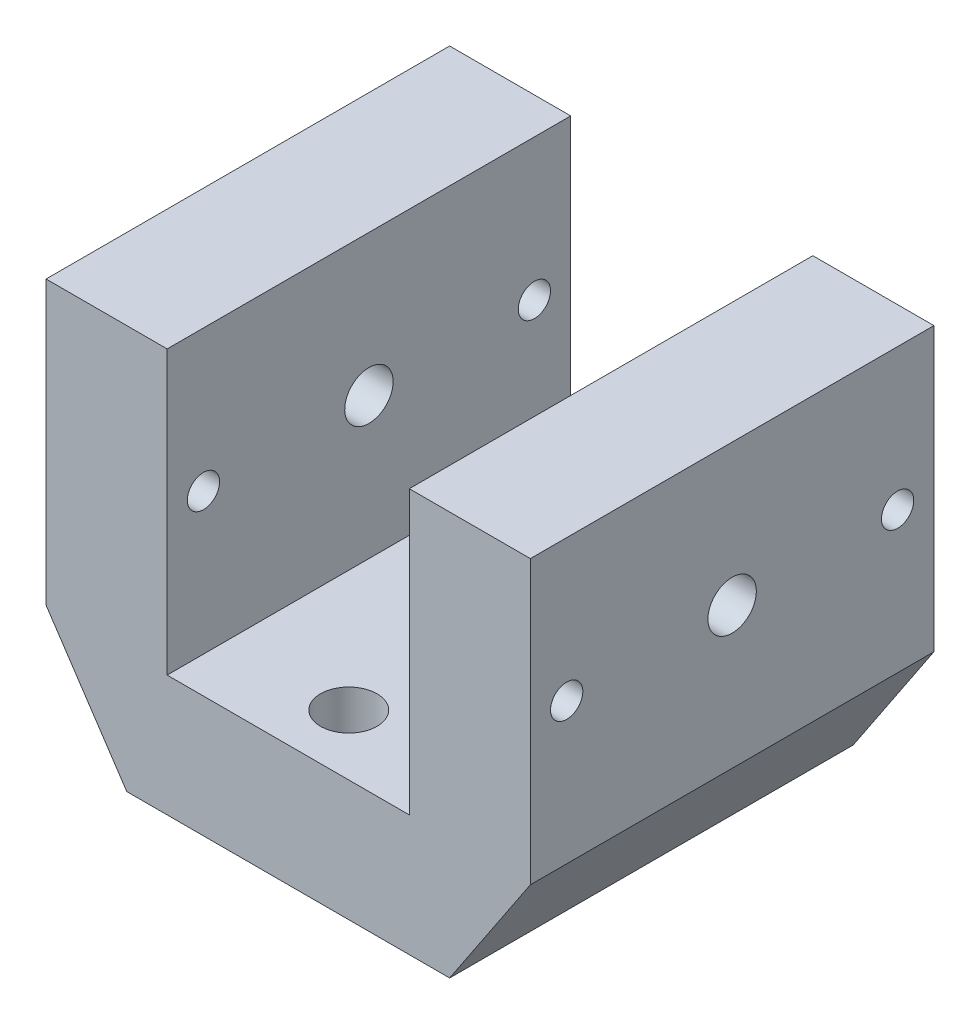
SolidWorks part; units mm, degrees
ref_plane "Płaszczyzna przednia" through (0, 0, 0) normal (0, 0, 1) x (1, 0, 0)
ref_plane "Płaszczyzna górna" through (0, 0, 0) normal (0, 1, 0) x (1, 0, 0)
ref_plane "Płaszczyzna prawa" through (0, 0, 0) normal (1, 0, 0) x (0, 0, -1)
sketch "Sketch1" plane through (0, 0, 0) normal (0, 0, 1) x (1, 0, 0)
  line L0 (-60, -50) -> (-60, 50)
  line L5 (-60, -50) -> (60, -50)
  line L7 (-60, 50) -> (60, 50)
  line L8 (60, -50) -> (60, 50)
  line L9 (-60, -50) -> (60, 50) construction
  line L10 (-60, 50) -> (60, -50) construction
  point P1 (0, 0)
  dimension "D1" = 100
  dimension "D2" = 120
extrude "Boss-Extrude1" add sketch "Sketch1" along normal blind 100
sketch "Sketch2" plane through (0, 0, 0) normal (0, 0, 1) x (1, 0, 0)
  line L24 (0, 50) -> (0, -50) construction
  line L25 (-60, -50) -> (60, -50) construction
  line L26 (-60, -20) -> (-40, -50)
  line L27 (-60, 50) -> (-60, -50) construction
  line L28 (30, 50) -> (30, -20)
  line L29 (-60, -20) -> (-60, -50)
  line L30 (-60, -50) -> (-40, -50)
  line L31 (-30, 50) -> (-30, -20)
  line L32 (60, 50) -> (-60, 50) construction
  line L33 (-30, -20) -> (30, -20)
  line L34 (-30, 50) -> (30, 50)
  line L35 (60, -50) -> (40, -50)
  line L36 (60, -20) -> (60, -50)
  line L37 (60, -20) -> (40, -50)
  point P18 (0, 0)
  dimension "D1" = 20
  dimension "D2" = 30
  dimension "D3" = 30
extrude "Cut-Extrude2" cut sketch "Sketch2" along normal through all both and the other way through all
sketch "Sketch3" plane through (0, 0, 0) normal (0, 1, 0) x (1, 0, 0)
  line L0 (-60, -50) -> (60, -50) construction
  line L1 (-60, -100) -> (-60, 0) construction
  line L2 (60, -100) -> (60, 0) construction
  line L3 (0, 0) -> (0, -100) construction
  line L4 (30, 0) -> (-30, 0) construction
  line L5 (-30, -100) -> (30, -100) construction
  circle A1 centre (0, -85) radius 4
  circle A2 centre (0, -15) radius 4
  dimension "D1" = 35
  dimension "D3" = 8
  dimension "D2" = 35
extrude "Cut-Extrude3" cut sketch "Sketch3" against normal through all both
sketch "Sketch5" plane through (0, 0, 0) normal (1, 0, 0) x (0, 0, -1)
  line L0 (-100, 15) -> (0, 15) construction
  line L1 (-100, -20) -> (-100, 50) construction
  line L2 (0, -20) -> (0, 50) construction
  circle A0 centre (-91, 15) radius 4
  circle A1 centre (-9, 15) radius 4
  dimension "D1" = 8
  dimension "D2" = 9
  dimension "D3" = 9
extrude "Cut-Extrude4" cut sketch "Sketch5" against normal through all both and the other way through all
sketch "Sketch6" plane through (0, 0, 0) normal (1, 0, 0) x (0, 0, -1)
  line L0 (-100, 15) -> (0, 15) construction
  line L1 (-100, -20) -> (-100, 50) construction
  line L2 (0, -20) -> (0, 50) construction
  line L3 (-50, 50) -> (-50, -20) construction
  line L4 (-100, 50) -> (0, 50) construction
  line L5 (-100, -20) -> (0, -20) construction
  circle A0 centre (-50, 15) radius 6
  dimension "D1" = 12
extrude "Cut-Extrude5" cut sketch "Sketch6" against normal through all and the other way through all
sketch "Sketch7" plane through (0, 0, 0) normal (0, 1, 0) x (1, 0, 0)
  circle A0 centre (0, -85) radius 7
  circle A1 centre (0, -15) radius 7
  dimension "D1" = 14
  dimension "D2" = 14
extrude "Cut-Extrude7" cut sketch "Sketch7" against normal blind 10 from surface at -20 starting at face at (-4, -20, 85)
